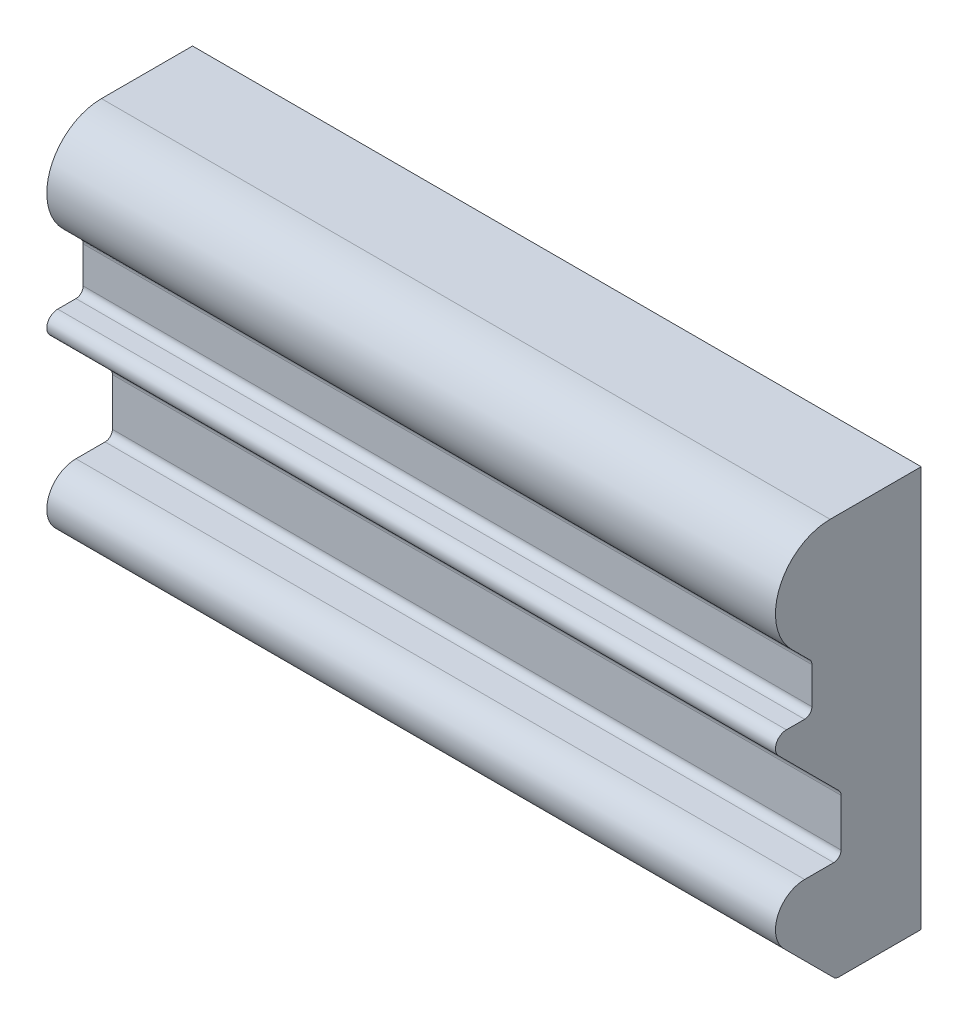
SolidWorks part; units mm, degrees
ref_plane "Front" through (0, 0, 0) normal (0, 0, 1) x (1, 0, 0)
ref_plane "Top" through (0, 0, 0) normal (0, 1, 0) x (1, 0, 0)
ref_plane "Right" through (0, 0, 0) normal (1, 0, 0) x (0, 0, -1)
sketch "Croquis1" plane through (0, 0, 0) normal (1, 0, 0) x (0, 0, -1)
  line L1 (0, 0) -> (-22.598, 0)
  line L2 (0, 0) -> (0, 110)
  line L3 (0, 110) -> (-25, 110)
  line L5 (-37, 65.9584) -> (-32, 65.9584)
  line L10 (-30, 77.9584) -> (-30, 67.9584)
  line L14 (-22, 29.8873) -> (-22, 42.8873)
  line L16 (-39.1213, 60.837) -> (-22.5858, 44.3015)
  line L17 (-32, 27.8873) -> (-24, 27.8873)
  line L18 (-35.6066, 84.3934) -> (-30.5858, 79.3726)
  line L19 (-37.6569, 14.2304) -> (-24.0122, 0.5858)
  arc A2 (-25, 110) -> (-35.6066, 84.3934) centre (-25, 95) ccw
  arc A3 (-32, 27.8873) -> (-37.6569, 14.2304) centre (-32, 19.8873) ccw
  arc A6 (-37, 65.9584) -> (-39.1213, 60.837) centre (-37, 62.9584) ccw
  arc A8 (-30.5858, 79.3726) -> (-30, 77.9584) centre (-32, 77.9584) cw
  arc A9 (-30, 67.9584) -> (-32, 65.9584) centre (-32, 67.9584) cw
  arc A10 (-22.5858, 44.3015) -> (-22, 42.8873) centre (-24, 42.8873) cw
  arc A11 (-22, 29.8873) -> (-24, 27.8873) centre (-24, 29.8873) cw
  arc A12 (-22.598, 0) -> (-24.0122, 0.5858) centre (-22.598, 2) cw
  point P0 (0, 0)
  point P11 (-30, 65.9584)
  dimension "D1" = 2
  dimension "D2" = 15
  dimension "D8" = 3
  dimension "D9" = 45
  dimension "D12" = 2
  dimension "D7" = 2
  dimension "D10" = 2
  dimension "D11" = 2
  dimension "D16" = 40
  dimension "D19" = 110
  dimension "D14" = 18
  dimension "D6" = 8
  dimension "D3" = 40
  dimension "D4" = 45
  dimension "D5" = 10
  dimension "D13" = 45
  dimension "D15" = 40
  dimension "D17" = 12
  dimension "D18" = 15
extrude "Saliente-Extruir1" add sketch "Croquis1" along normal blind 200
